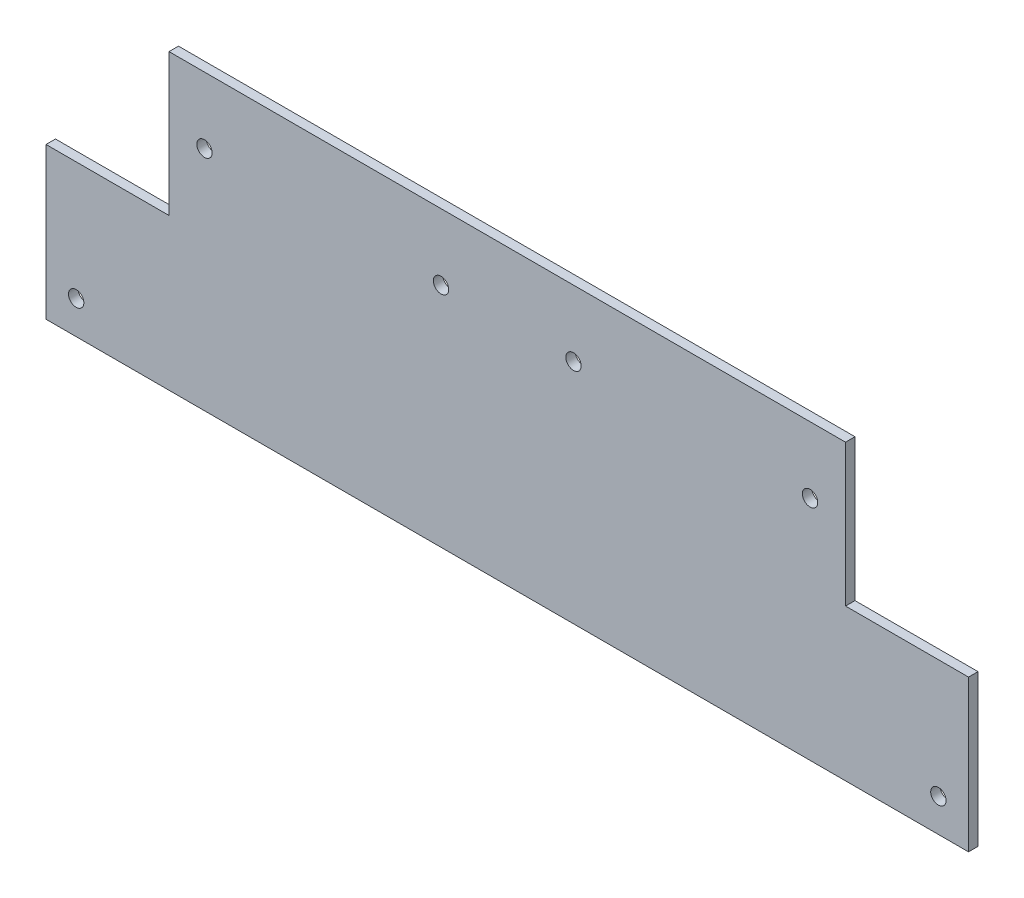
SolidWorks part; units mm, degrees
ref_plane "Alzado" through (0, 0, 0) normal (0, 0, 1) x (1, 0, 0)
ref_plane "Planta" through (0, 0, 0) normal (0, 1, 0) x (1, 0, 0)
ref_plane "Vista lateral" through (0, 0, 0) normal (1, 0, 0) x (0, 0, -1)
sketch "Croquis1" plane through (0, 0, 0) normal (0, 0, 1) x (1, 0, 0)
  line L0 (-97.5, 0) -> (97.5, 0)
  line L1 (97.5, 0) -> (97.5, 32)
  line L2 (97.5, 32) -> (71.5, 32)
  line L3 (71.5, 32) -> (71.5, 62)
  line L4 (71.5, 62) -> (-71.5, 62)
  line L5 (0, 68) -> (0, 0) construction
  line L6 (-71.5, 32) -> (-71.5, 62)
  line L7 (-97.5, 32) -> (-71.5, 32)
  line L8 (-97.5, 0) -> (-97.5, 32)
  circle A0 centre (91.125, 7) radius 1.625
  circle A1 centre (64, 48) radius 1.625
  circle A2 centre (14, 48) radius 1.625
  circle A3 centre (-14, 48) radius 1.625
  circle A4 centre (-64, 48) radius 1.625
  circle A5 centre (-91.125, 7) radius 1.625
  point P22 (0, 62)
  point P25 (0, 0)
  dimension "D1" = 3.25
  dimension "D2" = 7
  dimension "D3" = 6.375
  dimension "D5" = 25
  dimension "D7" = 16
  dimension "D9" = 7.5
  dimension "D10" = 50
  dimension "D4" = 97.5
  dimension "D6" = 26
  dimension "D8" = 30
  dimension "D11" = 14
extrude "Saliente-Extruir1" add sketch "Croquis1" along normal blind 2
